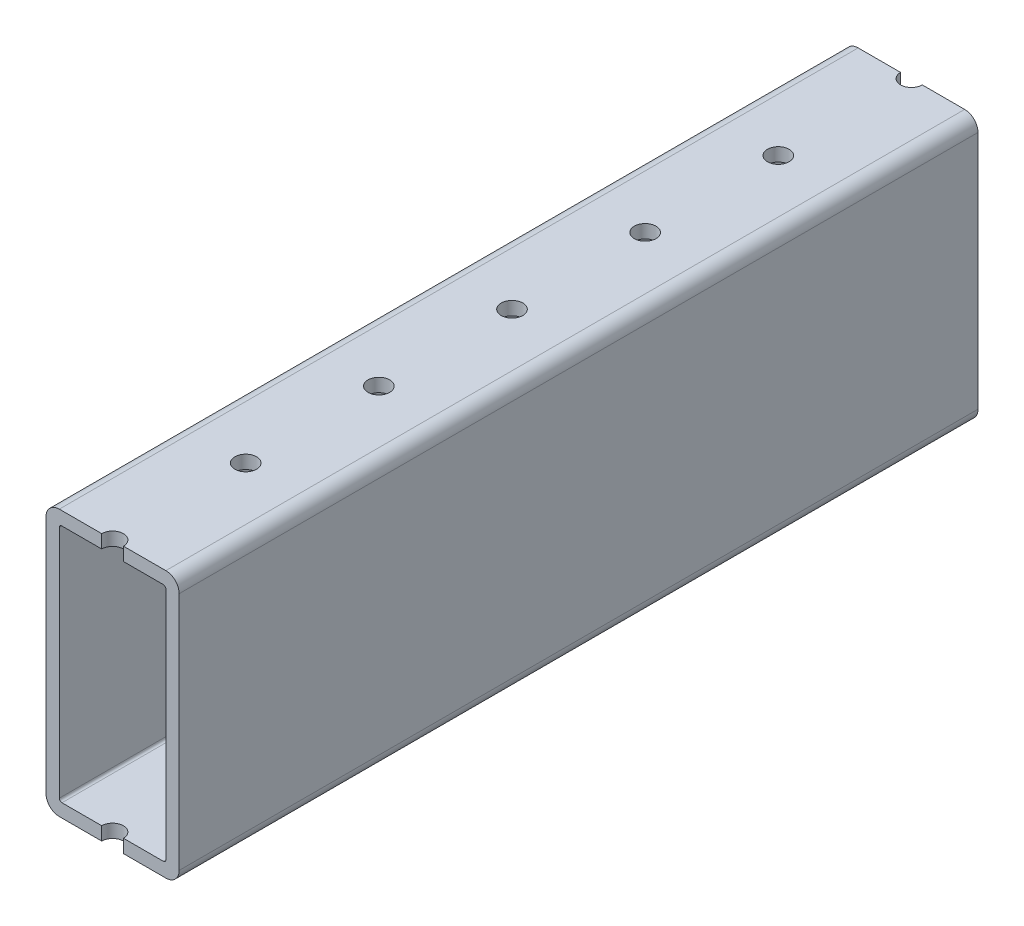
SolidWorks part; units mm, degrees
ref_plane "Front Plane" through (0, 0, 0) normal (0, 0, 1) x (1, 0, 0)
ref_plane "Top Plane" through (0, 0, 0) normal (0, 1, 0) x (1, 0, 0)
ref_plane "Right Plane" through (0, 0, 0) normal (1, 0, 0) x (0, 0, -1)
ref_plane "Plane1" through (12.7, 0, 0) normal (1, 0, 0) x (0, 0, -1)
sketch "Sketch1" plane through (12.7, 0, 0) normal (1, 0, 0) x (0, 0, -1)
  line L0 (76.2, -25.4) -> (76.2, 25.4)
  line L1 (76.2, 25.4) -> (-76.2, 25.4)
  line L2 (-76.2, 25.4) -> (-76.2, -25.4)
  line L3 (-76.2, -25.4) -> (76.2, -25.4)
  point P5 (0, 25.4)
  dimension "D1" = 50.8
  dimension "D2" = 25.4
  dimension "D3" = 152.4
extrude "Boss-Extrude1" add sketch "Sketch1" against normal blind 25.4
sketch "Sketch2" plane through (0, 0, -76.2) normal (0, 0, -1) x (-1, 0, 0)
  line L0 (10.16, -22.86) -> (10.16, 22.86)
  line L1 (10.16, 22.86) -> (-10.16, 22.86)
  line L2 (-10.16, 22.86) -> (-10.16, -22.86)
  line L3 (-10.16, -22.86) -> (10.16, -22.86)
extrude "Cut-Extrude1" cut sketch "Sketch2" against normal through all
hole_wizard "#6 Clearance Hole1" positions "Sketch4" profile "Sketch3" hole size "#6" standard "ANSI Inch"
sketch "Sketch4" plane through (0, -25.4, 0) normal (0, -1, 0) x (-1, 0, 0)
  point P0 (0, 711.2)
  point P1 (0, 736.6)
  point P2 (0, 685.8)
  point P3 (0, 660.4)
  point P4 (0, 635)
  point P5 (0, 609.6)
  point P6 (0, 584.2)
  point P7 (0, 558.8)
  point P8 (0, 533.4)
  point P9 (0, 508)
  point P10 (0, 482.6)
  point P11 (0, 457.2)
  point P12 (0, 431.8)
  point P13 (0, 406.4)
  point P14 (0, 381)
  point P15 (0, 355.6)
  point P16 (0, 330.2)
  point P17 (0, 304.8)
  point P18 (0, 279.4)
  point P19 (0, 254)
  point P20 (0, 228.6)
  point P21 (0, 203.2)
  point P22 (0, 177.8)
  point P23 (0, 152.4)
  point P24 (0, 127)
  point P25 (0, 101.6)
  point P26 (0, 76.2)
  point P27 (0, 50.8)
  point P28 (0, 25.4)
  point P29 (0, 0)
  point P30 (0, -25.4)
  point P31 (0, -50.8)
  point P32 (0, -76.2)
  point P33 (0, -101.6)
  point P34 (0, -127)
  point P35 (0, -152.4)
  point P36 (0, -177.8)
  point P37 (0, -203.2)
  point P38 (0, -228.6)
  point P39 (0, -254)
  point P40 (0, -279.4)
  point P41 (0, -304.8)
  point P42 (0, -330.2)
  point P43 (0, -355.6)
  point P44 (0, -381)
  point P45 (0, -406.4)
  point P46 (0, -431.8)
  point P47 (0, -457.2)
  point P48 (0, -482.6)
  point P49 (0, -508)
  point P50 (0, -533.4)
  point P51 (0, -558.8)
  point P52 (0, -584.2)
  point P53 (0, -609.6)
  point P54 (0, -635)
  point P55 (0, -660.4)
  point P56 (0, -685.8)
  point P57 (0, -711.2)
  point P58 (0, -736.6)
sketch "Sketch3" plane through (0, -25.4, -711.2) normal (1, 0, 0) x (0, 0, -1)
  line L0 (0, 0) -> (0, 50.8)
  line L1 (0, 50.8) -> (2.0701, 50.8)
  line L2 (2.0701, 50.8) -> (2.0701, 0)
  line L5 (2.0701, 0) -> (0, 0)
  line L11 (0, -6.35) -> (0, 107.95) construction
  dimension "Thru Hole Dia." = 4.1402
  dimension "Thru Hole Depth" = 50.8
hole_wizard "#6 Clearance Hole2" positions "Sketch6" profile "Sketch5" hole size "#6" standard "ANSI Inch"
sketch "Sketch6" plane through (0, 25.4, 0) normal (0, 1, 0) x (1, 0, 0)
  point P0 (0, 711.2)
  point P1 (0, 736.6)
  point P2 (0, 685.8)
  point P3 (0, 660.4)
  point P4 (0, 635)
  point P5 (0, 609.6)
  point P6 (0, 584.2)
  point P7 (0, 558.8)
  point P8 (0, 533.4)
  point P9 (0, 508)
  point P10 (0, 482.6)
  point P11 (0, 457.2)
  point P12 (0, 431.8)
  point P13 (0, 406.4)
  point P14 (0, 381)
  point P15 (0, 355.6)
  point P16 (0, 330.2)
  point P17 (0, 304.8)
  point P18 (0, 279.4)
  point P19 (0, 254)
  point P20 (0, 228.6)
  point P21 (0, 203.2)
  point P22 (0, 177.8)
  point P23 (0, 152.4)
  point P24 (0, 127)
  point P25 (0, 101.6)
  point P26 (0, 76.2)
  point P27 (0, 50.8)
  point P28 (0, 25.4)
  point P29 (0, 0)
  point P30 (0, -25.4)
  point P31 (0, -50.8)
  point P32 (0, -76.2)
  point P33 (0, -101.6)
  point P34 (0, -127)
  point P35 (0, -152.4)
  point P36 (0, -177.8)
  point P37 (0, -203.2)
  point P38 (0, -228.6)
  point P39 (0, -254)
  point P40 (0, -279.4)
  point P41 (0, -304.8)
  point P42 (0, -330.2)
  point P43 (0, -355.6)
  point P44 (0, -381)
  point P45 (0, -406.4)
  point P46 (0, -431.8)
  point P47 (0, -457.2)
  point P48 (0, -482.6)
  point P49 (0, -508)
  point P50 (0, -533.4)
  point P51 (0, -558.8)
  point P52 (0, -584.2)
  point P53 (0, -609.6)
  point P54 (0, -635)
  point P55 (0, -660.4)
  point P56 (0, -685.8)
  point P57 (0, -711.2)
  point P58 (0, -736.6)
sketch "Sketch5" plane through (0, 25.4, -711.2) normal (1, 0, 0) x (0, 0, 1)
  line L0 (0, 0) -> (0, 50.8)
  line L1 (0, 50.8) -> (2.0701, 50.8)
  line L2 (2.0701, 50.8) -> (2.0701, 0)
  line L5 (2.0701, 0) -> (0, 0)
  line L11 (0, -6.35) -> (0, 107.95) construction
  dimension "Thru Hole Dia." = 4.1402
  dimension "Thru Hole Depth" = 50.8
fillet "Fillet1" radius 0.5 4 edges at (10.16, 22.86, 0) (-10.16, -22.86, 0) (-10.16, 22.86, 0) (10.16, -22.86, 0)
fillet "Fillet2" radius 2.54 4 edges at (12.7, 25.4, 0) (-12.7, -25.4, 0) (12.7, -25.4, 0) (-12.7, 25.4, 0)
